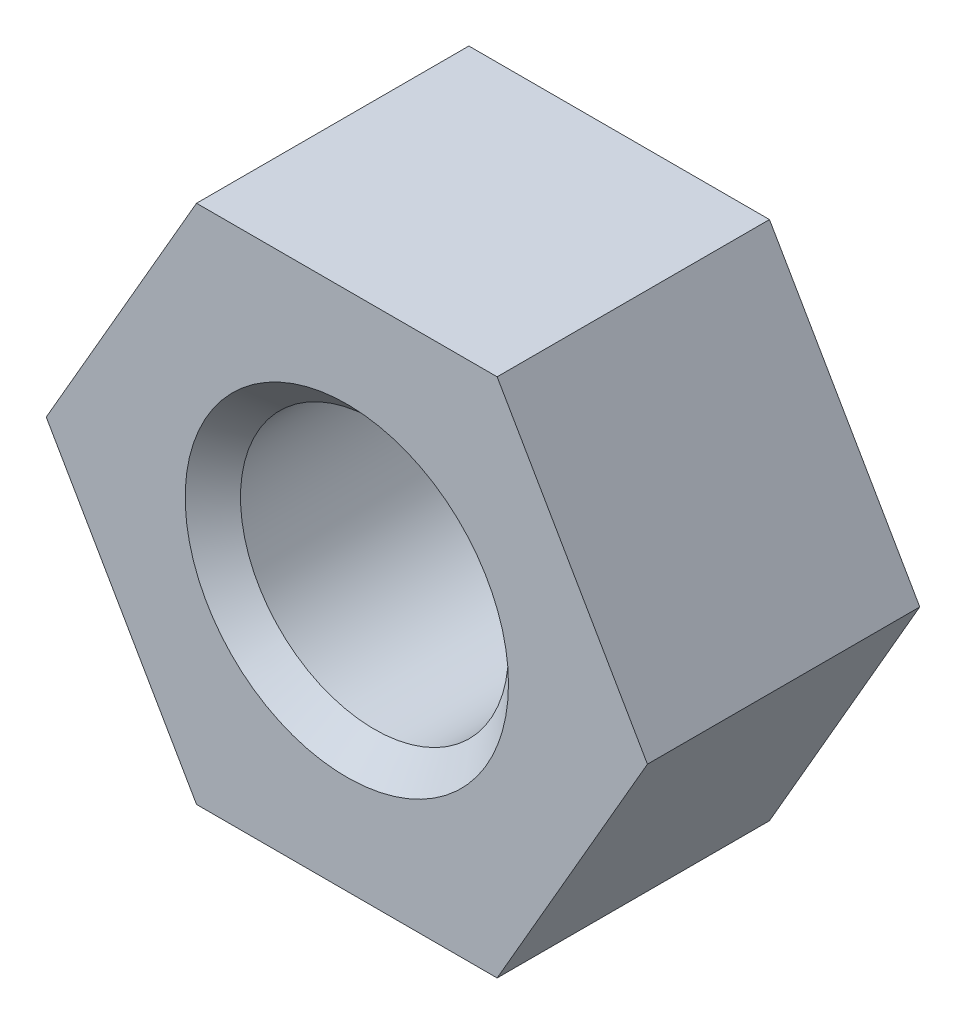
SolidWorks part; units mm, degrees
material "Сталь"
ref_plane "Спереди" through (0, 0, 0) normal (0, 0, 1) x (1, 0, 0)
ref_plane "Сверху" through (0, 0, 0) normal (0, 1, 0) x (1, 0, 0)
ref_plane "Справа" through (0, 0, 0) normal (1, 0, 0) x (0, 0, -1)
sketch "Эскиз1" plane through (0, 0, 0) normal (0, 0, 1) x (1, 0, 0)
  line L1 (-3.7528, 6.5) -> (-7.5056, 0)
  line L2 (-7.5056, 0) -> (-3.7528, -6.5)
  line L3 (-3.7528, -6.5) -> (3.7528, -6.5)
  line L4 (3.7528, -6.5) -> (7.5056, 0)
  line L5 (7.5056, 0) -> (3.7528, 6.5)
  line L6 (3.7528, 6.5) -> (-3.7528, 6.5)
  circle A0 centre (0, 0) radius 3.3455
  circle A1 centre (0, 0) radius 6.5 construction
  dimension "D1" = 6.691
  dimension "D2" = 13
extrude "Бобышка-Вытянуть1" add sketch "Эскиз1" along normal blind 6.8
cosmetic thread "Условное изображение резьбы1" parameters "D2"=8
chamfer "Фаска1" distance 0.6905 angle 45 2 edges at (3.3455, 0, 0) (3.3455, 0, 6.8)
